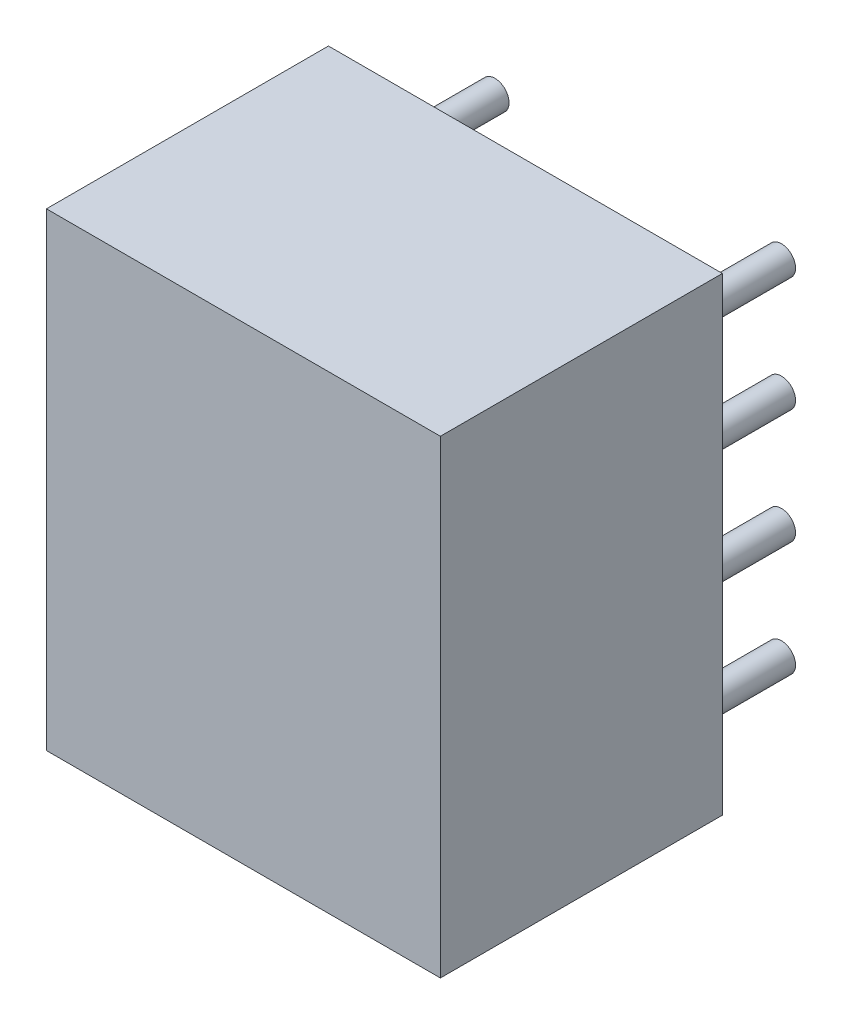
SolidWorks part; units mm, degrees
ref_plane "Front Plane" through (0, 0, 0) normal (0, 0, 1) x (1, 0, 0)
ref_plane "Top Plane" through (0, 0, 0) normal (0, 1, 0) x (1, 0, 0)
ref_plane "Right Plane" through (0, 0, 0) normal (1, 0, 0) x (0, 0, -1)
sketch "Sketch1" plane through (0, 0, 0) normal (0, 0, 1) x (1, 0, 0)
  line L0 (-0.9525, 7.366) -> (-0.9525, -0.9525)
  line L1 (-0.9525, -0.9525) -> (6.0325, -0.9525)
  line L2 (6.0325, -0.9525) -> (6.0325, 7.366)
  line L3 (6.0325, 7.366) -> (-0.9525, 7.366)
extrude "Component_Outline" add sketch "Sketch1" along normal blind 5 separate body
sketch "Sketch2" plane through (0, 0, 0) normal (0, 0, 1) x (1, 0, 0)
  circle A0 centre (5.08, 0) radius 0.25
extrude "1" add sketch "Sketch2" against normal blind 2 separate body
sketch "Sketch3" plane through (0, 0, 0) normal (0, 0, 1) x (1, 0, 0)
  circle A0 centre (5.08, 2.032) radius 0.25
extrude "Boss-Extrude3" add sketch "Sketch3" against normal blind 2 separate body
sketch "Sketch4" plane through (0, 0, 0) normal (0, 0, 1) x (1, 0, 0)
  circle A0 centre (5.08, 4.064) radius 0.25
extrude "Boss-Extrude4" add sketch "Sketch4" against normal blind 2 separate body
sketch "Sketch5" plane through (0, 0, 0) normal (0, 0, 1) x (1, 0, 0)
  circle A0 centre (5.08, 6.096) radius 0.25
extrude "Boss-Extrude5" add sketch "Sketch5" against normal blind 2 separate body
sketch "Sketch6" plane through (0, 0, 0) normal (0, 0, 1) x (1, 0, 0)
  circle A0 centre (0, 0) radius 0.25
extrude "2" add sketch "Sketch6" against normal blind 2 separate body
sketch "Sketch7" plane through (0, 0, 0) normal (0, 0, 1) x (1, 0, 0)
  circle A0 centre (0, 2.032) radius 0.25
extrude "3" add sketch "Sketch7" against normal blind 2 separate body
sketch "Sketch8" plane through (0, 0, 0) normal (0, 0, 1) x (1, 0, 0)
  circle A0 centre (0, 4.064) radius 0.25
extrude "4" add sketch "Sketch8" against normal blind 2 separate body
sketch "Sketch9" plane through (0, 0, 0) normal (0, 0, 1) x (1, 0, 0)
  circle A0 centre (0, 6.096) radius 0.25
extrude "5" add sketch "Sketch9" against normal blind 2 separate body
sketch3d "3DSketch1"
  line L0 (0, 0, 0) -> (1, 0, 0)
  line L1 (0, 0, 0) -> (0, 1, 0)
  line L2 (0, 0, 0) -> (0, 0, 1)
  point P0 (0, 0, 0)
